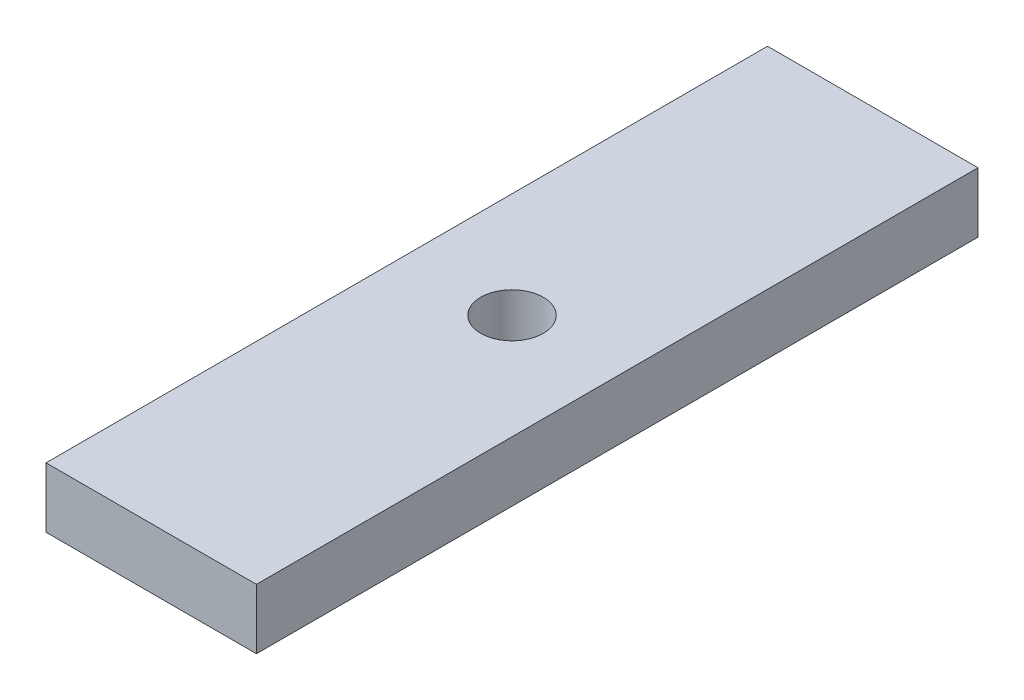
SolidWorks part; units mm, degrees
ref_plane "Front Plane" through (0, 0, 0) normal (0, 0, 1) x (1, 0, 0)
ref_plane "Top Plane" through (0, 0, 0) normal (0, 1, 0) x (1, 0, 0)
ref_plane "Right Plane" through (0, 0, 0) normal (1, 0, 0) x (0, 0, -1)
sketch "Sketch1" plane through (0, 0, 0) normal (0, 1, 0) x (1, 0, 0)
  line L0 (0, 0) -> (35, 0)
  line L1 (35, 0) -> (35, 120)
  line L2 (35, 120) -> (0, 120)
  line L3 (0, 120) -> (0, 0)
  line L4 (0, 60) -> (35, 60)
  circle A0 centre (17.5, 60) radius 5.2058
extrude "Boss-Extrude1" add sketch "Sketch1" along normal blind 10 contours A0 L4 L1 L2 L3 | A0 L4 L3 L0 L1
